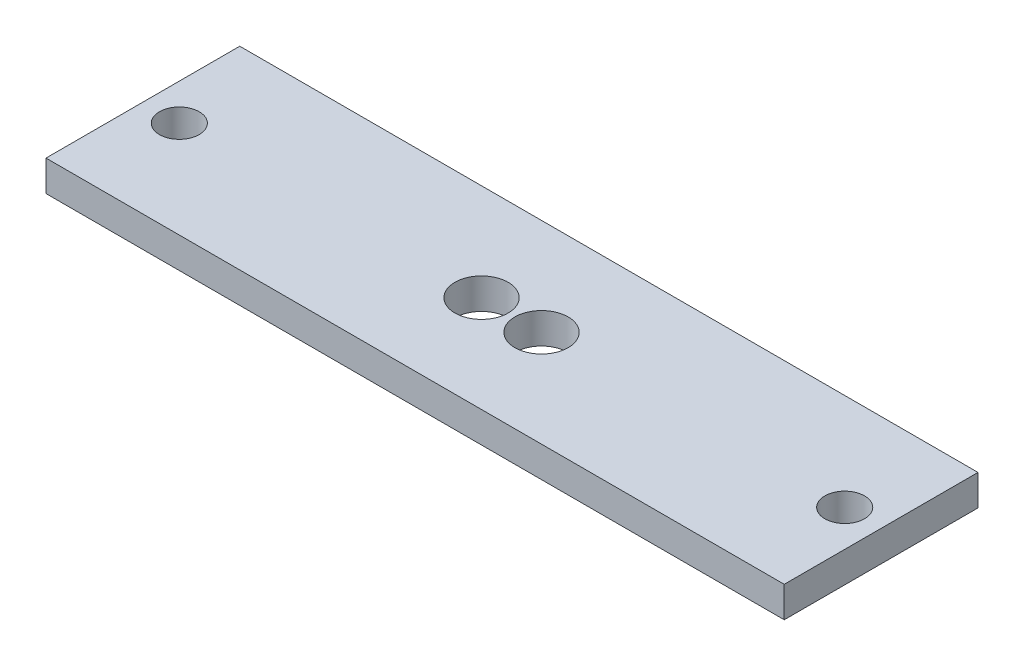
SolidWorks part; units mm, degrees
ref_plane "Front Plane" through (0, 0, 0) normal (0, 0, 1) x (1, 0, 0)
ref_plane "Top Plane" through (0, 0, 0) normal (0, 1, 0) x (1, 0, 0)
ref_plane "Right Plane" through (0, 0, 0) normal (1, 0, 0) x (0, 0, -1)
sketch "Sketch1" plane through (0, 0, 0) normal (0, 1, 0) x (1, 0, 0)
  line L0 (38.1, -9.5245) -> (38.1, 10.4755)
  line L1 (38.1, 10.4755) -> (-38.1, 10.4755)
  line L2 (-38.1, 10.4755) -> (-38.1, -9.5245)
  line L3 (-38.1, -9.5245) -> (38.1, -9.5245)
  circle A0 centre (3.048, 0.4755) radius 2.75
  circle A1 centre (-3.1437, 0.4755) radius 2.75
  circle A2 centre (-34.3404, 0.4755) radius 2.0497
  circle A3 centre (34.3404, 0.4755) radius 2.0497
extrude "Boss-Extrude1" add sketch "Sketch1" along normal blind 3.175
